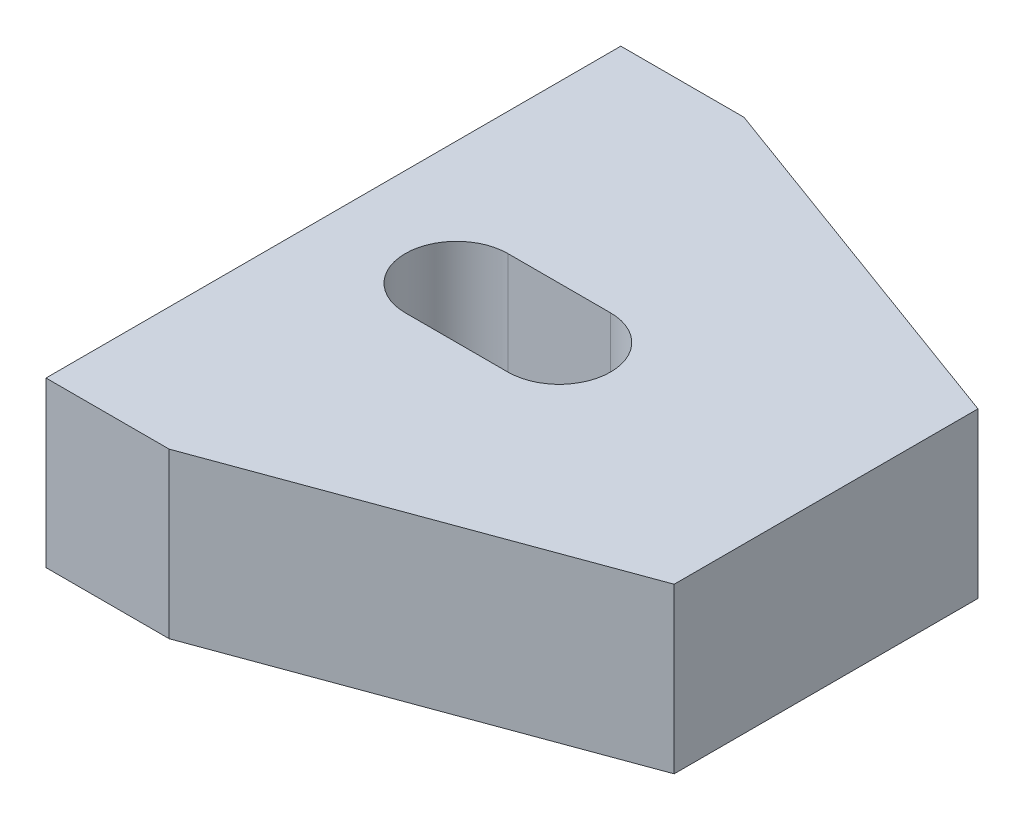
SolidWorks part; units mm, degrees
material "ABS"
ref_plane "Front Plane" through (0, 0, 0) normal (0, 0, 1) x (1, 0, 0)
ref_plane "Top Plane" through (0, 0, 0) normal (0, 1, 0) x (1, 0, 0)
ref_plane "Right Plane" through (0, 0, 0) normal (1, 0, 0) x (0, 0, -1)
sketch "Sketch1" plane through (0, 0, 0) normal (0, 1, 0) x (1, 0, 0)
  line L0 (-15.24, 8.89) -> (-15.24, -8.89)
  line L1 (-15.24, -8.89) -> (-11.43, -8.89)
  line L2 (-11.43, -8.89) -> (0, -4.699)
  line L3 (0, -4.699) -> (0, 4.699)
  line L4 (0, 4.699) -> (-11.43, 8.89)
  line L5 (-11.43, 8.89) -> (-15.24, 8.89)
  line L6 (3.81, -1000.8756) -> (3.81, 48999.1244) construction
  line L7 (-11.43, 0) -> (-8.255, 0) construction
  line L8 (-11.43, 1.5875) -> (-8.255, 1.5875)
  line L9 (-11.43, -1.5875) -> (-8.255, -1.5875)
  arc A0 (-11.43, 1.5875) -> (-11.43, -1.5875) centre (-11.43, 0) ccw
  arc A1 (-8.255, -1.5875) -> (-8.255, 1.5875) centre (-8.255, 0) ccw
  point P11 (-9.8425, 0)
  dimension "D3" = 1.5875
  dimension "D1" = 15.24
  dimension "D2" = 3.81
  dimension "D4" = 3.175
  dimension "D5" = 3.81
  dimension "D6" = 9.398
  dimension "D7" = 17.78
  dimension "D8" = 3.81
extrude "Boss-Extrude1" add sketch "Sketch1" along normal blind 5.08
